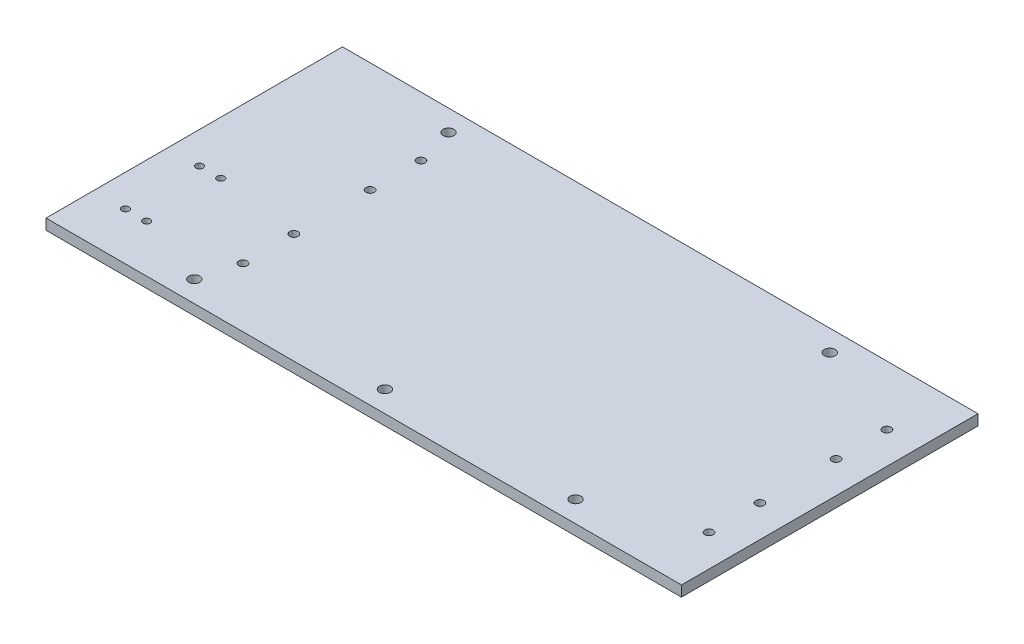
SolidWorks part; units mm, degrees
material "6061-T6 (SS)"
ref_plane "Front Plane" through (0, 0, 0) normal (0, 0, 1) x (1, 0, 0)
ref_plane "Top Plane" through (0, 0, 0) normal (0, 1, 0) x (1, 0, 0)
ref_plane "Right Plane" through (0, 0, 0) normal (1, 0, 0) x (0, 0, -1)
sketch "Sketch1" plane through (0, 0, 0) normal (0, 1, 0) x (1, 0, 0)
  line L1 (-190.5, -88.9) -> (190.5, -88.9)
  line L2 (-190.5, -88.9) -> (-190.5, 88.9)
  line L3 (-190.5, 88.9) -> (190.5, 88.9)
  line L4 (190.5, -88.9) -> (190.5, 88.9)
  point P4 (0, 88.9)
  point P6 (-190.5, 0)
  dimension "D1" = 381
  dimension "D2" = 177.8
extrude "Plate" add sketch "Sketch1" along normal blind 6.35
sketch "Sketch2" plane through (0, 0, 88.9) normal (0, 0, 1) x (1, 0, 0)
  line L1 (-190.5, 0) -> (190.5, 0)
  line L2 (-190.5, 0) -> (-190.5, 31.75)
  line L3 (-190.5, 31.75) -> (190.5, 31.75)
  line L4 (190.5, 0) -> (190.5, 31.75)
  dimension "D1" = 31.75
extrude "Boss-Extrude2" [suppressed] add sketch "Sketch2" along normal blind 6.35
sketch "Sketch3" [suppressed] plane through (0, 0, 95.25) normal (0, 0, 1) x (1, 0, 0)
  line L0 (0, 0) -> (0, 31.75) construction
  line L1 (-190.5, 0) -> (190.5, 0) construction
  line L2 (190.5, 31.75) -> (-190.5, 31.75) construction
  circle A0 centre (0, 19.05) radius 3.175
  circle A1 centre (-127, 19.05) radius 3.175
  circle A2 centre (127, 19.05) radius 3.175
  dimension "D1" = 6.35
  dimension "D2" = 12.7
  dimension "D3" = 127
  dimension "D4" = 127
extrude "Cut-Extrude1" [suppressed] cut sketch "Sketch3" against normal up to surface (6.35 mm away)
sketch "Sketch4" plane through (0, 0, 0) normal (0, -1, 0) x (1, 0, 0)
  line L2 (190.5, -88.9) -> (-190.5, -88.9) construction
  circle A0 centre (0, 76.2) radius 3.2639
  circle A1 centre (-114.3, 76.2) radius 3.2639
  circle A2 centre (114.3, 76.2) radius 3.2639
  circle A3 centre (-114.3, -76.2) radius 3.2639
  circle A5 centre (114.3, -76.2) radius 3.2639
  dimension "D2" = 6.5278
  dimension "D3" = 114.3
  dimension "D5" = 12.7
  dimension "D1" = 76.2
  dimension "D4" = 114.3
extrude "ChassisMountingHoles" cut sketch "Sketch4" against normal up to surface (6.35 mm away) up to face at (0, 6.35, 0)
sketch "Sketch5" plane through (0, 0, 0) normal (0, -1, 0) x (1, 0, 0)
  line L0 (190.5, 88.9) -> (190.5, -88.9) construction
  line L3 (0, 0) -> (0, 229.4543) construction
  line L4 (171.45, 22.86) -> (171.45, 53.34) construction
  line L5 (0, 0) -> (353.5615, 0) construction
  circle A2 centre (171.45, 53.34) radius 2.5019
  circle A8 centre (171.45, 22.86) radius 2.5019
  circle A14 centre (-107.95, 53.34) radius 2.5019
  circle A15 centre (-107.95, 22.86) radius 2.5019
  circle A16 centre (171.45, -53.34) radius 2.5019
  circle A17 centre (171.45, -22.86) radius 2.5019
  circle A18 centre (-107.95, -22.86) radius 2.5019
  circle A19 centre (-107.95, -53.34) radius 2.5019
  dimension "D1" = 5.0038
  dimension "D2" = 19.05
  dimension "D5" = 30.48
  dimension "D6" = 279.4
extrude "LeadScrewGuideMounts" cut sketch "Sketch5" against normal up to surface (6.35 mm away) up to face at (114.3, 6.35, -79.4639)
sketch "Sketch6" plane through (0, 0, 0) normal (0, -1, 0) x (1, 0, 0)
  line L0 (-190.5, -88.9) -> (-190.5, 88.9) construction
  line L1 (-190.5, 88.9) -> (190.5, 88.9) construction
  circle A0 centre (-171.45, 60.325) radius 2.1527
  circle A1 centre (-158.75, 60.325) radius 2.1527
  circle A2 centre (-171.45, 15.875) radius 2.1527
  circle A3 centre (-158.75, 15.875) radius 2.1527
  dimension "D3" = 4.3053
  dimension "D1" = 12.7
  dimension "D2" = 19.05
  dimension "D4" = 44.45
  dimension "D5" = 28.575
extrude "LeadScrewMotorMount" cut sketch "Sketch6" against normal up to surface (6.35 mm away) up to face at (-107.95, 6.35, -25.3619)
